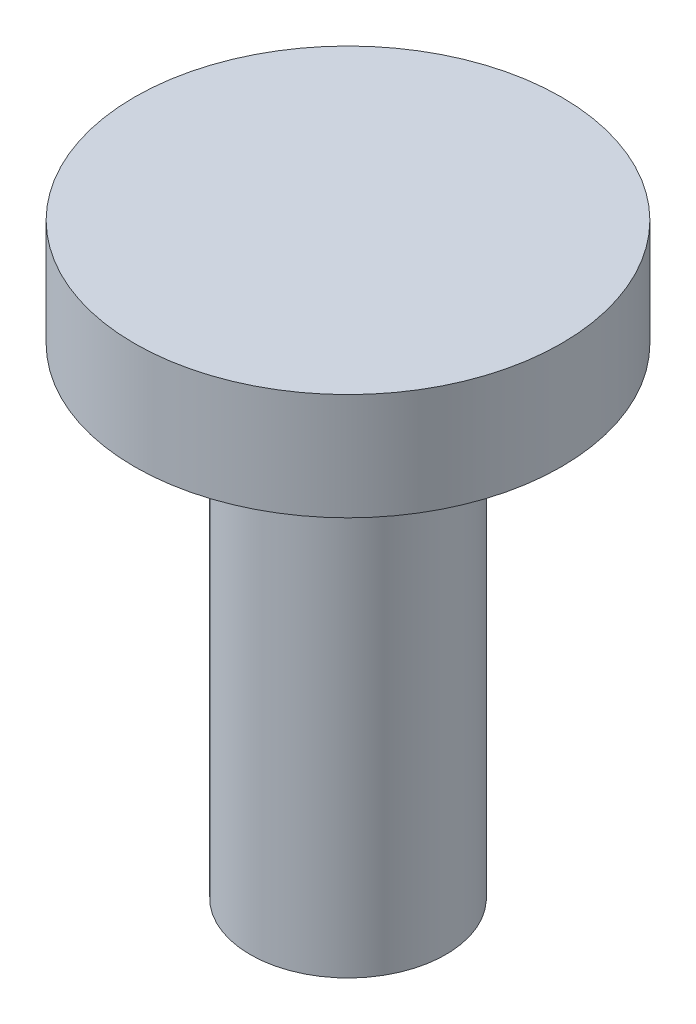
SolidWorks part; units mm, degrees
ref_plane "Front" through (0, 0, 0) normal (0, 0, 1) x (1, 0, 0)
ref_plane "Top" through (0, 0, 0) normal (0, 1, 0) x (1, 0, 0)
ref_plane "Right" through (0, 0, 0) normal (1, 0, 0) x (0, 0, -1)
sketch "Sketch1" plane through (0, 0, 0) normal (0, 1, 0) x (1, 0, 0)
  circle A0 centre (0, 0) radius 10
  dimension "D1" = 20
extrude "Boss-Extrude1" add sketch "Sketch1" along normal blind 45
scale "축척1" scale about centroid uniform scaling yes scale factor 0.3
sketch "스케치1" plane through (0, 29.25, 0) normal (0, 1, 0) x (1, 0, 0)
  circle A0 centre (0, 0) radius 6
  dimension "D1" = 12
extrude "보스-돌출1" add sketch "스케치1" along normal blind 3
sketch "스케치2" plane through (0, 15.75, 0) normal (0, -1, 0) x (1, 0, 0)
  circle A0 centre (0, 0) radius 3
  circle A1 centre (0, 0) radius 2.75
  dimension "D1" = 6
  dimension "D2" = 0.25
extrude "컷-돌출1" cut sketch "스케치2" against normal up to surface (13.5 mm away) up to face at (0, 29.25, 3)
